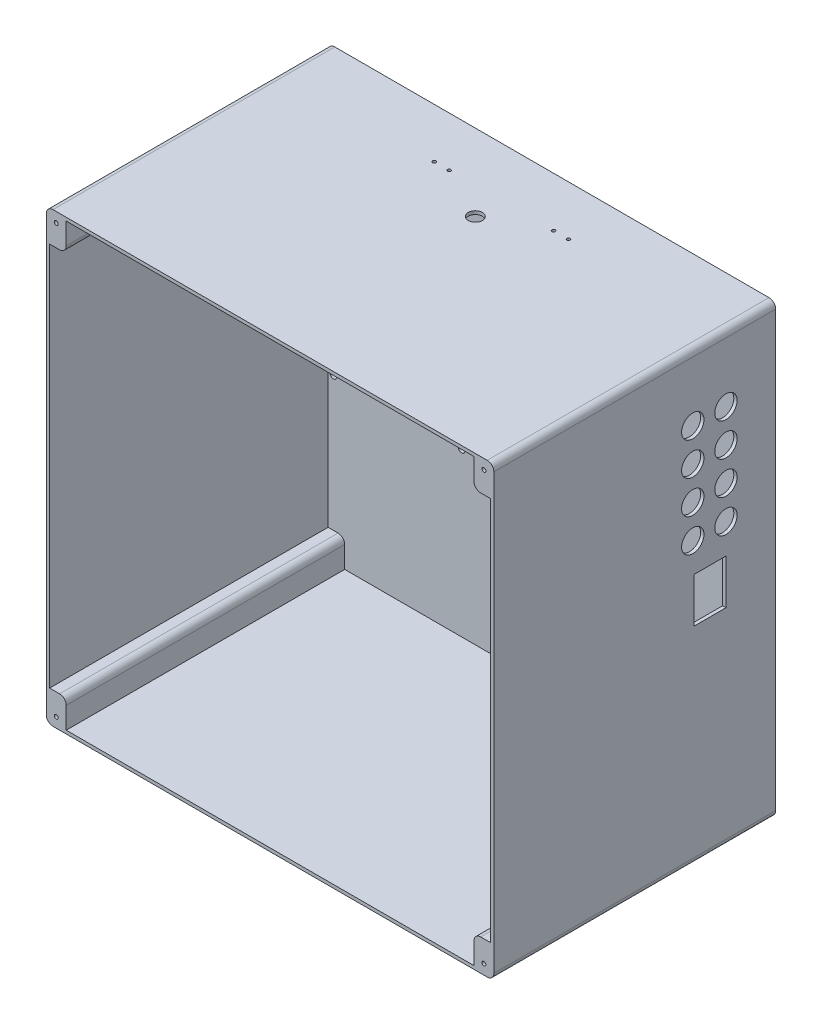
SolidWorks part; units mm, degrees
ref_plane "Plan de face" through (0, 0, 0) normal (0, 0, 1) x (1, 0, 0)
ref_plane "Plan de dessus" through (0, 0, 0) normal (0, 1, 0) x (1, 0, 0)
ref_plane "Plan de droite" through (0, 0, 0) normal (1, 0, 0) x (0, 0, -1)
sketch "Esquisse1" plane through (0, 0, 0) normal (0, 0, 1) x (1, 0, 0)
  line L1 (0, 0) -> (270, 0)
  line L2 (0, 0) -> (0, -270)
  line L3 (0, -270) -> (270, -270)
  line L4 (270, 0) -> (270, -270)
  dimension "D1" = 270
  dimension "D2" = 270
extrude "Extrusion1" add sketch "Esquisse1" along normal blind 170
fillet "Congé2" radius 4 4 edges at (0, -270, 85) (270, -270, 85) (0, 0, 85) (270, 0, 85)
sketch "Esquisse2" plane through (0, 0, 170) normal (0, 0, 1) x (1, 0, 0)
  line L0 (12, -2) -> (12, -19)
  line L1 (12, -19) -> (2, -19)
  line L2 (2, -19) -> (2, -251)
  line L3 (2, -251) -> (12, -251)
  line L4 (12, -251) -> (12, -268)
  line L5 (12, -268) -> (258, -268)
  line L6 (258, -268) -> (258, -251)
  line L7 (258, -251) -> (268, -251)
  line L8 (268, -251) -> (268, -19)
  line L9 (268, -19) -> (258, -19)
  line L10 (258, -19) -> (258, -2)
  line L11 (258, -2) -> (12, -2)
  line L12 (0, -4) -> (0, -266) construction
  line L13 (4, -270) -> (266, -270) construction
  line L14 (270, -266) -> (270, -4) construction
  line L16 (266, 0) -> (4, 0) construction
  dimension "D1" = 17
  dimension "D2" = 10
  dimension "D3" = 2
  dimension "D4" = 2
  dimension "D5" = 2
  dimension "D6" = 2
extrude "Extrusion2" cut sketch "Esquisse2" against normal blind 168
fillet "Congé3" radius 4 4 edges at (258, -19, 86) (258, -251, 86) (12, -19, 86) (12, -251, 86)
hole_wizard "Trou taraudé #4-481" positions "Esquisse3D1" profile "Esquisse4" tap size "#4-48" standard "Ansi Pouces"
sketch3d "Esquisse3D1"
  line L0 (0, -4, 170) -> (0, -266, 170) construction
  line L1 (270, -266, 170) -> (270, -4, 170) construction
  line L2 (266, 0, 170) -> (4, 0, 170) construction
  line L3 (4, -270, 170) -> (266, -270, 170) construction
  point P0 (6, -6, 170)
  point P2 (264, -6, 170)
  point P4 (264, -264, 170)
  point P6 (6, -264, 170)
  dimension "D1" = 6
  dimension "D2" = 6
  dimension "D3" = 6
  dimension "D4" = 6
  dimension "D5" = 6
  dimension "D6" = 6
  dimension "D7" = 6
  dimension "D8" = 6
sketch "Esquisse4" plane through (6, -6, 170) normal (1, 0, 0) x (0, -1, 0)
  line L0 (0, 0) -> (0, 45.7135)
  line L1 (0, 45.7135) -> (1.1874, 45)
  line L2 (1.1874, 45) -> (1.1874, 0)
  line L5 (1.1874, 0) -> (0, 0)
  line L10 (0, 45.7135) -> (-1.1875, 45) construction
  line L11 (0, -6.35) -> (0, 107.95) construction
  dimension "Diamètre du trou pour taraudage" = 2.3749
  dimension "Profondeur du trou pour taraudage" = 45
  dimension "Angle de pointe" = 118
cosmetic thread "Filetage de perçage1" parameters "D1"=40, "D2"=2.8448
cosmetic thread "Filetage de perçage2" parameters "D1"=40, "D2"=2.8448
cosmetic thread "Filetage de perçage3" parameters "D1"=40, "D2"=2.8448
cosmetic thread "Filetage de perçage4" parameters "D1"=40, "D2"=2.8448
sketch "Esquisse5" plane through (2, 0, 0) normal (1, 0, 0) x (0, 0, -1)
  line L0 (0, -266) -> (0, -4) construction
  line L1 (-47, -75.328) -> (-33, -75.328)
  line L2 (-47, -75.328) -> (-47, -91.328)
  line L3 (-47, -91.328) -> (-33, -91.328)
  line L4 (-33, -75.328) -> (-33, -91.328)
  dimension "D1" = 14
  dimension "D2" = 16
  dimension "D3" = 33
extrude "Enlèv. mat.-Extru.1" cut sketch "Esquisse5" against normal through all
sketch "Esquisse6" plane through (270, -440, 0) normal (-1, 0, 0) x (0, 0, -1)
  line L0 (24.7185, -400) -> (-120.7742, -400) construction
  line L2 (-170, -440) -> (0, -440) construction
  line L5 (0, -174) -> (0, -436) construction
  circle A1 centre (-50, -400) radius 6.75
  circle A2 centre (-30, -400) radius 6.75
  dimension "D1" = 13.5
  dimension "D2" = 13.5
  dimension "D3" = 40
  dimension "D4" = 30
  dimension "D7" = 20
extrude "Enlèv. mat.-Extru.6" cut sketch "Esquisse6" against normal blind 10 and the other way blind 10
pattern_linear "Répétition linéaire3" count 4 spacing 20 along (0, -1, 0) of "Enlèv. mat.-Extru.6"
sketch "Esquisse7" plane through (0, 0, 0) normal (0, 1, 0) x (-1, 0, 0)
  line L0 (-266, 0) -> (-4, 0) construction
  line L1 (-4, 46.2) -> (-266, 46.2) construction
  line L2 (-4, 0) -> (-4, 170) construction
  line L3 (-266, 170) -> (-266, 0) construction
  circle A0 centre (-135, 46.2) radius 4.25
  dimension "D1" = 8.5
  dimension "D2" = 46.2
extrude "Enlèv. mat.-Extru.7" cut sketch "Esquisse7" against normal blind 3
sketch "Esquisse8" plane through (0, 0, 0) normal (0, 0, -1) x (-1, 0, 0)
  circle A0 centre (-154.5, -50) radius 2
  circle A1 centre (-115.5, -50) radius 2
  circle A2 centre (-115.5, -90) radius 2
  circle A3 centre (-154.5, -90) radius 2
extrude "Enlèv. mat.-Extru.8" cut sketch "Esquisse8" against normal through all
sketch "Esquisse9" plane through (0, 0, 0) normal (0, 1, 0) x (-1, 0, 0)
  line L0 (-266, 0) -> (-4, 0) construction
  line L1 (-175, 30) -> (-166, 30) construction
  line L2 (-270, 0) -> (-270, 170) construction
  line L3 (-94, 30) -> (-103, 30) construction
  circle A0 centre (-175, 30) radius 1
  circle A1 centre (-166, 30) radius 1
  circle A2 centre (-103, 30) radius 1
  circle A3 centre (-94, 30) radius 1
  dimension "D1" = 30
  dimension "D2" = 9
  dimension "D3" = 95
  dimension "D4" = 9
  dimension "D5" = 63
extrude "Enlèv. mat.-Extru.9" cut sketch "Esquisse9" against normal blind 10
sketch "Esquisse10" plane through (270, 0, 0) normal (1, 0, 0) x (0, 0, -1)
  line L0 (0, -270) -> (-170, -270) construction
  line L1 (-49.2, -118) -> (-30, -118)
  line L2 (-49.2, -118) -> (-49.2, -145)
  line L3 (-49.2, -145) -> (-30, -145)
  line L4 (-30, -118) -> (-30, -145)
  line L5 (0, -266) -> (0, -4) construction
  dimension "D1" = 19.2
  dimension "D2" = 27
  dimension "D3" = 125
  dimension "D4" = 30
extrude "Enlèv. mat.-Extru.10" cut sketch "Esquisse10" against normal blind 10
sketch "Esquisse11" plane through (0, -270, 0) normal (0, -1, 0) x (1, 0, 0)
  line L0 (4, 0) -> (266, 0) construction
  line L1 (270, 170) -> (270, 0) construction
  circle A0 centre (245, 10) radius 5
  dimension "D1" = 10
  dimension "D2" = 10
  dimension "D3" = 25
extrude "Enlèv. mat.-Extru.11" cut sketch "Esquisse11" against normal blind 10
sketch "Esquisse12" plane through (0, 0, 2) normal (0, 0, 1) x (1, 0, 0)
  circle A0 centre (82.5, -31.8344) radius 2
  circle A1 centre (5.5, -31.8344) radius 2
  circle A2 centre (5.1923, -169.8344) radius 2
  circle A3 centre (82.5, -169.8344) radius 2
  dimension "D1" = 4
  dimension "D2" = 4
  dimension "D3" = 4
  dimension "D4" = 4
extrude "Enlèv. mat.-Extru.12" cut sketch "Esquisse12" against normal blind 10
